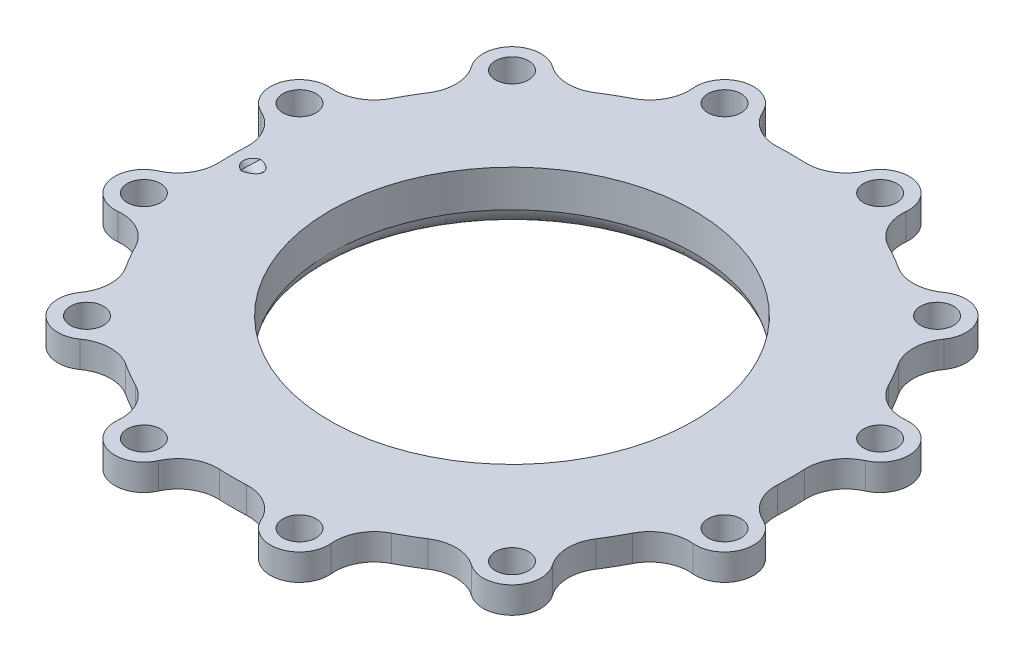
SolidWorks part; units mm, degrees
material "Nickel"
ref_plane "Front Plane" through (0, 0, 0) normal (0, 0, 1) x (1, 0, 0)
ref_plane "Top Plane" through (0, 0, 0) normal (0, 1, 0) x (1, 0, 0)
ref_plane "Right Plane" through (0, 0, 0) normal (1, 0, 0) x (0, 0, -1)
sketch "Sketch2" plane through (0, 0, 0) normal (0, 0, 1) x (1, 0, 0)
  line L0 (43.848, 12.7) -> (43.848, 3.81)
  line L1 (43.848, 12.7) -> (79.375, 12.7)
  line L2 (59.723, 6.35) -> (59.723, 8.0645)
  line L4 (0, 45.0513) -> (0, -47.1704) construction
  line L5 (59.723, 8.0645) -> (50.198, 8.0645)
  line L6 (48.928, 1.27) -> (48.928, 0)
  line L7 (48.928, 0) -> (46.388, 0)
  line L9 (59.723, 6.35) -> (79.375, 6.35)
  line L10 (79.375, 6.35) -> (79.375, 12.7)
  line L11 (50.198, 8.0645) -> (50.198, -6.0335) construction
  spline S0 degree 3 poles (48.928, 1.27) (48.928, 2.3622) (47.7561, 4.7871) (49.4813, 8.0645) (50.198, 8.0645) knots 0 0 0 0 0.567934 1 1 1 1
  spline S1 degree 2 poles (46.388, 0) (44.3884, 1.4142) (43.848, 3.81) knots 0 0 0 1 1 1
  point P17 (47.658, 0)
  dimension "D11" = 1.6667
  dimension "D12" = 2.673
  dimension "D13" = 1.27
  dimension "D2" = 9.525
  dimension "D3" = 1.7145
  dimension "D4" = 3.81
  dimension "D5" = 6.35
  dimension "D6" = 79.375
  dimension "D7" = 12.7
  dimension "D8" = 50.198
  dimension "D9" = 1.27
  dimension "D10" = 1.6071
  dimension "D14" = 1.6184
  dimension "D15" = 6.35
  dimension "D16" = 2.54
revolve "Revolve1" add sketch "Sketch2" angle 360 about L4
fillet "Fillet1" radius 1.27 1 edges at (-59.723, 8.0645, 0)
sketch "Sketch5" plane through (0, 0, 0) normal (0, 0, 1) x (1, 0, 0)
  line L0 (-54.61, 6.35) -> (-73.7665, 6.35) construction
  line L1 (-54.61, 6.35) -> (-55.3883, 5.6969)
  line L2 (-54.61, 6.35) -> (-59.876, 12.6258)
  line L4 (-55.3883, 5.6969) -> (-68.4497, 21.263)
  line L5 (-79.8785, 34.8832) -> (-68.4497, 21.263) construction
  line L6 (-54.61, 6.35) -> (-54.61, 26.5181) construction
  line L7 (-66.4067, 22.9773) -> (-59.876, 15.1943)
  line L8 (-59.876, 15.1943) -> (-59.876, 12.6258)
  line L9 (-66.4067, 22.9773) -> (-68.4497, 21.263)
  dimension "D1" = 50
  dimension "D2" = 1.016
  dimension "D3" = 38.1
  dimension "D4" = 6.35
  dimension "D5" = 54.61
  dimension "D6" = 2.667
  dimension "D7" = 20.32
  dimension "D8" = 10.16
revolve "Cut-Revolve2" cut sketch "Sketch5" angle 360 about L4
sketch "Sketch11" [suppressed] plane through (0, 0, 0) normal (0, 0, 1) x (1, 0, 0)
  line L0 (-54.61, 6.35) -> (-66.3666, 20.3609) construction
  line L1 (-54.61, 6.35) -> (-69.2769, 6.35) construction
  line L2 (-55.9363, 6.35) -> (-71.1246, 24.4507)
  dimension "D1" = 50
  dimension "D2" = 54.61
  dimension "D3" = 6.35
  dimension "D4" = 1.016
ref_plane "Plane5" through (0, 0, 0) normal (-0.7071, 0.7071, 0) x (0.7071, 0.7071, 0)
sketch "Sketch19" plane through (0, 12.7, 0) normal (0, 1, 0) x (1, 0, 0)
  line L0 (0, 0) -> (0, 180.1699) construction
  circle A0 centre (0, 0) radius 72.39 construction
  point P4 (0, 72.39)
  dimension "D1" = 144.78
hole_wizard "Hole2" positions "Sketch20" profile "Sketch21" legacy end condition through all
sketch "Sketch20" plane through (0, 12.7, 0) normal (0, 1, 0) x (1, 0, 0)
  line L1 (0, 0) -> (-18.7359, 69.9234)
  line L3 (0, 0) -> (0, 180.1699) construction
  point P0 (-18.7359, 69.9234)
  dimension "D1" = 72.39
  dimension "D2" = 15
sketch "Sketch21" plane through (-18.7359, 12.7, -69.9234) normal (1, 0, 0) x (0, 0, 1)
  line L0 (0, 0) -> (0, 12.7)
  line L1 (0, 12.7) -> (4, 12.7)
  line L2 (4, 12.7) -> (4, 0)
  line L3 (4, 0) -> (0, 0)
  line L4 (0, 110) -> (0, -10) construction
  dimension "Diameter" = 8
  dimension "Depth" = 12.7
pattern_circular "CirPattern2" count 12 over 360 about axis through (0, 0, 0) along (0, 1, 0) of "Hole2"
sketch "Sketch22" plane through (0, 12.7, 0) normal (0, 1, 0) x (1, 0, 0)
  arc A0 (76.6704, -20.5438) -> (72.8098, -12.3752) centre (69.9234, -18.7359) ccw
  arc A1 (72.8098, 12.3752) -> (76.6704, 20.5438) centre (69.9234, 18.7359) ccw
  arc A2 (67.2318, -3.2426) -> (67.2318, 3.2426) centre (0, 0) ccw
  arc A3 (67.2318, -3.2426) -> (72.8098, -12.3752) centre (76.7458, -3.7015) ccw
  arc A4 (76.6704, -20.5438) -> (76.6704, 20.5438) centre (0, 0) ccw
  arc A5 (72.8098, 12.3752) -> (67.2318, 3.2426) centre (76.7458, 3.7015) ccw
  circle A6 centre (0, 0) radius 79.375 construction
  dimension "D1" = 134.62
  dimension "D2" = 19.05
extrude "Cut-Extrude1" cut sketch "Sketch22" against normal up to next (6.35 mm away)
pattern_circular "CirPattern3" count 12 over 360 about axis through (0, 0, 0) along (0, 1, 0) of "Cut-Extrude1"
